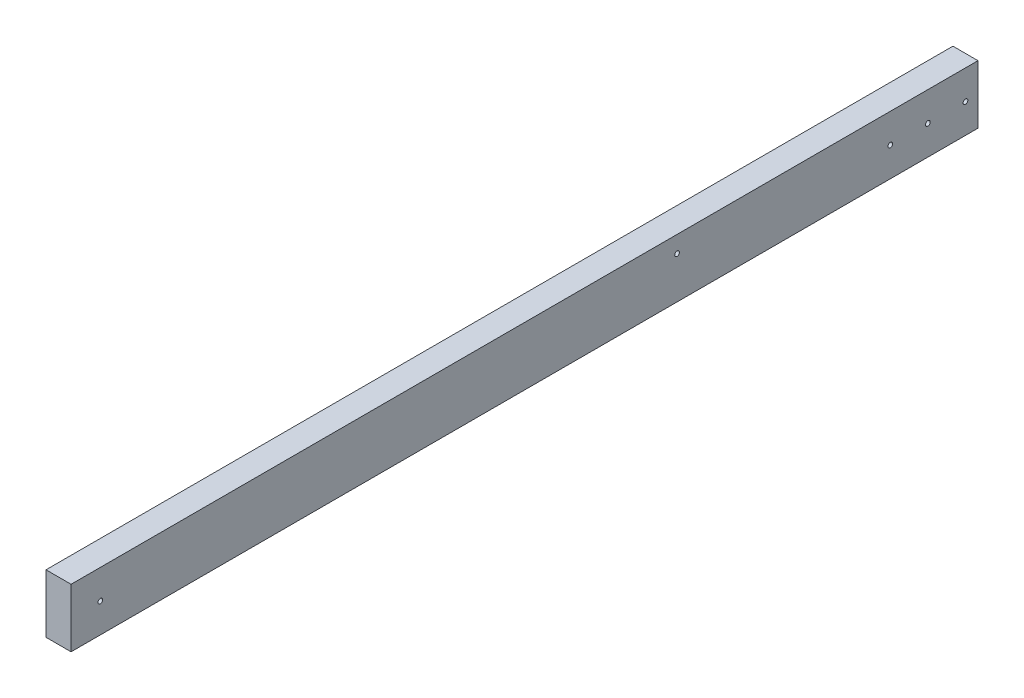
SolidWorks part; units mm, degrees
material "Pine"
ref_plane "Front Plane" through (0, 0, 0) normal (0, 0, 1) x (1, 0, 0)
ref_plane "Top Plane" through (0, 0, 0) normal (0, 1, 0) x (1, 0, 0)
ref_plane "Right Plane" through (0, 0, 0) normal (1, 0, 0) x (0, 0, -1)
sketch "Sketch1" plane through (0, 0, 0) normal (0, 0, 1) x (1, 0, 0)
  line L1 (-19.05, -44.45) -> (19.05, -44.45)
  line L2 (-19.05, -44.45) -> (-19.05, 44.45)
  line L3 (-19.05, 44.45) -> (19.05, 44.45)
  line L4 (19.05, -44.45) -> (19.05, 44.45)
  line L5 (-19.05, -44.45) -> (19.05, 44.45) construction
  line L6 (-19.05, 44.45) -> (19.05, -44.45) construction
  point P0 (0, 0)
  dimension "D1" = 88.9
  dimension "D2" = 38.1
extrude "Boss-Extrude1" add sketch "Sketch1" along normal blind 1377.95
sketch "Sketch3" plane through (19.05, 0, 0) normal (1, 0, 0) x (0, 0, -1)
  line L0 (0, -44.45) -> (0, 44.45) construction
  line L1 (-1377.95, -44.45) -> (-1377.95, 44.45) construction
  point P0 (-19.05, 0)
  point P1 (-76.2, 0)
  point P2 (-133.35, 0)
  point P6 (-1333.5, 0)
  point P7 (-457.2, 19.05)
  point P10 (0, 0)
  point P11 (-457.4556, 21.1623)
  dimension "D1" = 19.05
  dimension "D2" = 57.15
  dimension "D3" = 57.15
  dimension "D4" = 19.05
  dimension "D5" = 44.45
  dimension "D6" = 876.3
hole_wizard "9/32 (0.28125) Diameter Hole1" positions "Sketch4" profile "Sketch5" hole size "9/32" standard "ANSI Inch" end condition through all
sketch "Sketch4" plane through (19.05, 0, 0) normal (1, 0, 0) x (0, 0, -1)
  point P0 (-19.05, 0)
  point P3 (-76.2, 0)
  point P6 (-133.35, 0)
  point P10 (-1333.5, 0)
  point P13 (-457.2, 19.05)
sketch "Sketch5" plane through (19.05, 0, 19.05) normal (0, 1, 0) x (0, 0, -1)
  line L0 (0, 0) -> (0, 38.1)
  line L1 (0, 38.1) -> (3.5719, 38.1)
  line L2 (3.5719, 38.1) -> (3.5719, 0)
  line L5 (3.5719, 0) -> (0, 0)
  line L11 (0, -6.35) -> (0, 107.95) construction
  dimension "Thru Hole Dia." = 7.1437
  dimension "Thru Hole Depth" = 38.1
